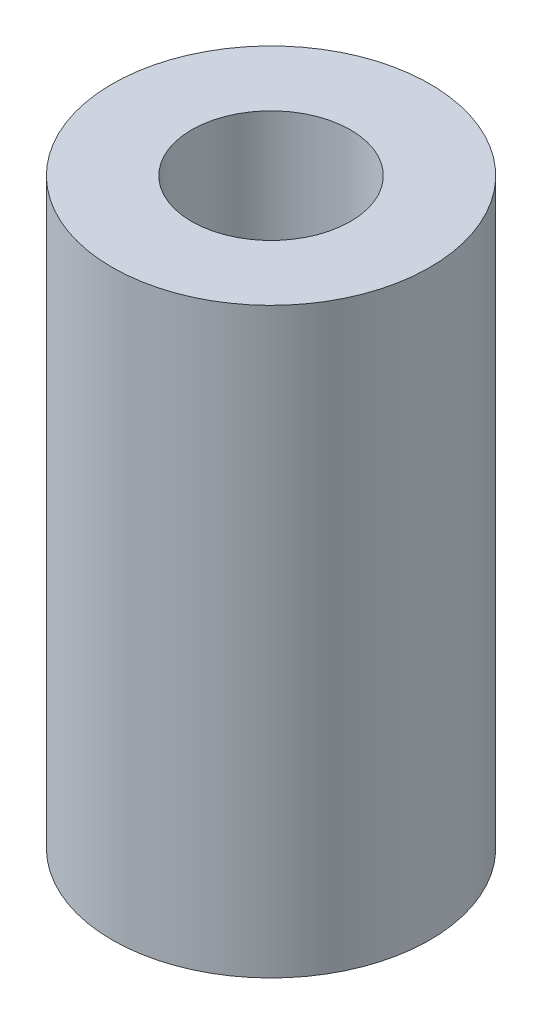
SolidWorks part; units mm, degrees
ref_plane "Plan de face" through (0, 0, 0) normal (0, 0, 1) x (1, 0, 0)
ref_plane "Plan de dessus" through (0, 0, 0) normal (0, 1, 0) x (1, 0, 0)
ref_plane "Plan de droite" through (0, 0, 0) normal (1, 0, 0) x (0, 0, -1)
sketch "Esquisse1" plane through (0, 0, 0) normal (0, 1, 0) x (1, 0, 0)
  circle A0 centre (0, 0) radius 6
  dimension "D1" = 12
extrude "Boss.-Extru.1" add sketch "Esquisse1" along normal blind 22
sketch "Esquisse3" plane through (0, 22, 0) normal (0, 1, 0) x (1, 0, 0)
  circle A0 centre (0, 0) radius 3
  dimension "D1" = 6
extrude "Enlèv. mat.-Extru.3" cut sketch "Esquisse3" against normal blind 22 contours A0
